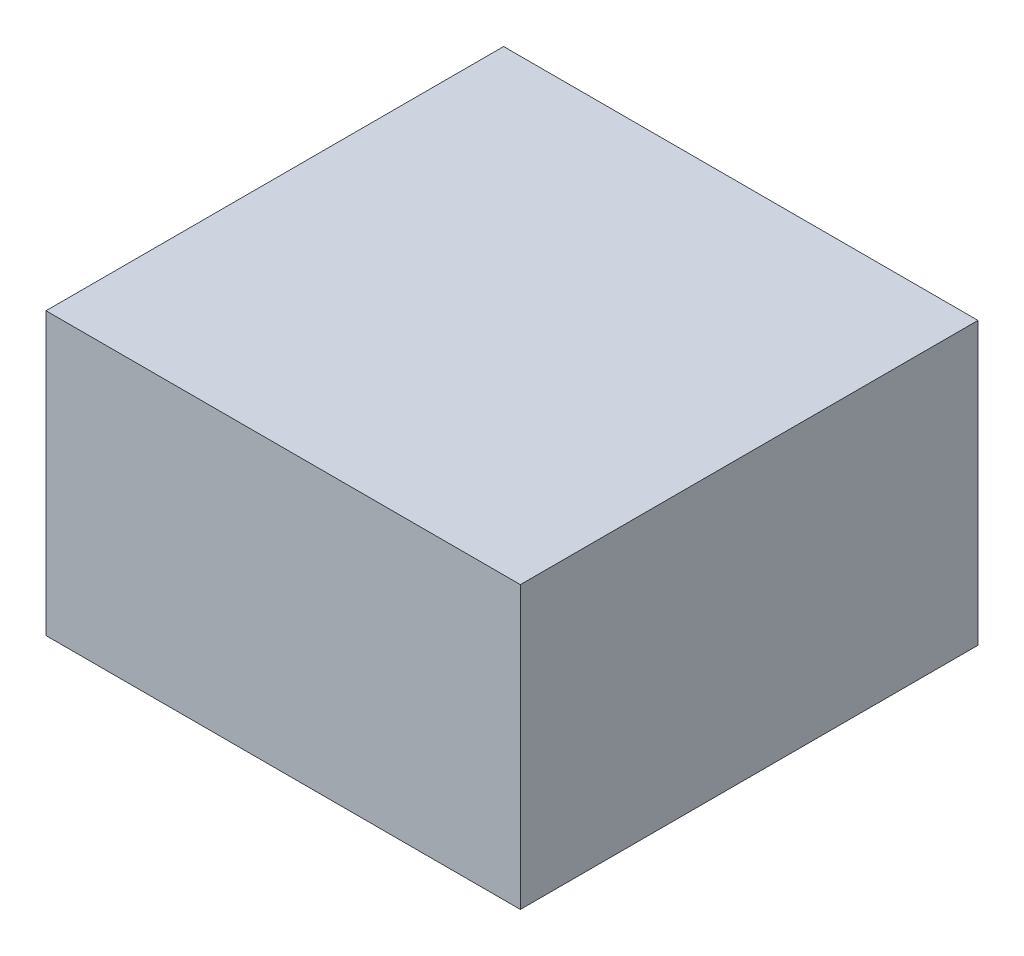
SolidWorks part; units mm, degrees
material "1060 Alloy"
ref_plane "Front Plane" through (0, 0, 0) normal (0, 0, 1) x (1, 0, 0)
ref_plane "Top Plane" through (0, 0, 0) normal (0, 1, 0) x (1, 0, 0)
ref_plane "Right Plane" through (0, 0, 0) normal (1, 0, 0) x (0, 0, -1)
sketch "Sketch1" plane through (0, 0, 0) normal (0, 1, 0) x (1, 0, 0)
  line L1 (-212.5, 205) -> (212.5, 205)
  line L2 (-212.5, 205) -> (-212.5, -205)
  line L3 (-212.5, -205) -> (212.5, -205)
  line L4 (212.5, 205) -> (212.5, -205)
  line L5 (-212.5, 205) -> (212.5, -205) construction
  line L6 (-212.5, -205) -> (212.5, 205) construction
  point P0 (0, 0)
  dimension "D1" = 425
  dimension "D2" = 410
extrude "Bottom" add sketch "Sketch1" along normal blind 3.175
sketch "Sketch2" plane through (0, 3.175, 0) normal (0, 1, 0) x (1, 0, 0)
  line L0 (0, 202.714) -> (0, -202.714) construction
  line L1 (-210.214, 0) -> (210.214, 0) construction
  line L2 (-1.143, 202.714) -> (-1.143, -202.714)
  line L3 (1.143, 202.714) -> (1.143, -202.714)
  line L4 (-210.214, -1.143) -> (210.214, -1.143)
  line L5 (-210.214, 1.143) -> (210.214, 1.143)
  line L8 (210.214, -202.714) -> (210.214, 202.714)
  line L9 (210.214, 202.714) -> (-210.214, 202.714)
  line L10 (-210.214, 202.714) -> (-210.214, -202.714)
  line L11 (-210.214, -202.714) -> (210.214, -202.714)
  line L12 (210.214, -202.714) -> (210.214, 202.714)
  line L13 (210.214, 202.714) -> (-210.214, 202.714)
  line L14 (-210.214, 202.714) -> (-210.214, -202.714)
  line L15 (-210.214, -202.714) -> (210.214, -202.714)
  line L16 (212.5, -205) -> (212.5, 205)
  line L17 (212.5, 205) -> (-212.5, 205)
  line L18 (-212.5, 205) -> (-212.5, -205)
  line L19 (-212.5, -205) -> (212.5, -205)
  line L20 (212.5, -205) -> (212.5, 205)
  line L21 (212.5, 205) -> (-212.5, 205)
  line L22 (-212.5, 205) -> (-212.5, -205)
  line L23 (-212.5, -205) -> (212.5, -205)
  line M9 (212.5, -205) -> (212.5, 205)
  line M10 (212.5, 205) -> (-212.5, 205)
  line M11 (-212.5, 205) -> (-212.5, -205)
  line M12 (-212.5, -205) -> (212.5, -205)
  dimension "D1" = 2.286
  dimension "D2" = 0
  dimension "D3" = 1.143
  dimension "D4" = 1.143
  dimension "D5" = 1.143
  dimension "D6" = 1.143
extrude "Sides" add sketch "Sketch2" along normal blind 246.6 contours L5 L14 L4 L2 | L5 L2 L4 L3 | L2 L15 L3 L4 | L4 L12 L5 L3 | L3 L13 L2 L5 | L15 L14 L13 L12 M12 M9 M10 M11
sketch "Sketch3" plane through (0, 249.775, 0) normal (0, 1, 0) x (1, 0, 0)
  line L4 (-212.5, 205) -> (-212.5, -205) construction
  line L5 (-212.5, -205) -> (212.5, -205) construction
  line L6 (212.5, -205) -> (212.5, 205) construction
  line L7 (212.5, 205) -> (-212.5, 205) construction
  line L8 (-212.5, 205) -> (-212.5, -205)
  line L9 (-212.5, -205) -> (212.5, -205)
  line L10 (212.5, -205) -> (212.5, 205)
  line L11 (212.5, 205) -> (-212.5, 205)
extrude "Top" add sketch "Sketch3" along normal blind 2.286
sketch "Sketch4" plane through (-212.5, 0, 0) normal (-1, 0, 0) x (0, 0, 1)
  line L0 (-205, 252.061) -> (-205, 0) construction
  line L1 (-205, 232.061) -> (-143, 232.061)
  line L2 (-205, 232.061) -> (-205, 132.061)
  line L3 (-205, 132.061) -> (-143, 132.061)
  line L4 (-143, 232.061) -> (-143, 132.061)
  line L5 (-135.4, 232.061) -> (-73.4, 232.061)
  line L6 (-135.4, 232.061) -> (-135.4, 132.061)
  line L7 (-135.4, 132.061) -> (-73.4, 132.061)
  line L8 (-73.4, 232.061) -> (-73.4, 132.061)
  line L9 (-65.8, 232.061) -> (-3.8, 232.061)
  line L10 (-65.8, 232.061) -> (-65.8, 132.061)
  line L11 (-65.8, 132.061) -> (-3.8, 132.061)
  line L12 (-3.8, 232.061) -> (-3.8, 132.061)
  line L13 (3.8, 232.061) -> (65.8, 232.061)
  line L14 (3.8, 232.061) -> (3.8, 132.061)
  line L15 (3.8, 132.061) -> (65.8, 132.061)
  line L16 (65.8, 232.061) -> (65.8, 132.061)
  line L17 (73.4, 232.061) -> (135.4, 232.061)
  line L18 (73.4, 232.061) -> (73.4, 132.061)
  line L19 (73.4, 132.061) -> (135.4, 132.061)
  line L20 (135.4, 232.061) -> (135.4, 132.061)
  line L21 (143, 232.061) -> (205, 232.061)
  line L22 (143, 232.061) -> (143, 132.061)
  line L23 (143, 132.061) -> (205, 132.061)
  line L24 (205, 232.061) -> (205, 132.061)
  line L25 (205, 252.061) -> (205, 0) construction
  line L26 (-205, 252.061) -> (205, 252.061) construction
  dimension "D1" = 62
  dimension "D2" = 100
  dimension "D3" = 62
  dimension "D4" = 62
  dimension "D5" = 62
  dimension "D6" = 62
  dimension "D7" = 62
  dimension "D8" = 7.6
  dimension "D9" = 7.6
  dimension "D10" = 7.6
  dimension "D11" = 7.6
  dimension "D12" = 20
split line "IGBTs"
